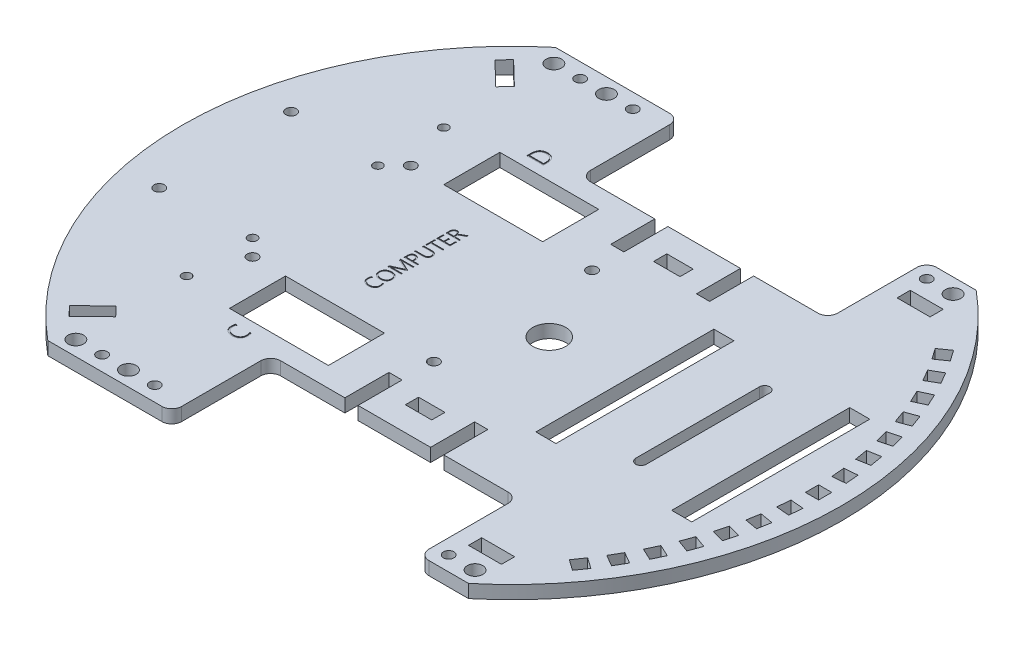
SolidWorks part; units mm, degrees
material "Oak"
ref_plane "Front Plane" through (0, 0, 0) normal (0, 0, 1) x (1, 0, 0)
ref_plane "Top Plane" through (0, 0, 0) normal (0, 1, 0) x (1, 0, 0)
ref_plane "Right Plane" through (0, 0, 0) normal (1, 0, 0) x (0, 0, -1)
sketch "Sketch1" plane through (0, 0, 0) normal (0, 1, 0) x (1, 0, 0)
  line L0 (-63.8044, 77) -> (63.8044, 77)
  line L1 (-63.8044, -77) -> (63.8044, -77)
  circle A0 centre (0, 0) radius 100
  dimension "D1" = 200
  dimension "D2" = 154
extrude "Basis" add sketch "Sketch1" along normal blind 4 contours L1 A0 L0
sketch "Sketch2" plane through (0, 4, 0) normal (0, 1, 0) x (1, 0, 0)
  line L0 (90.817, -6.1912) -> (94.8018, -6.5398)
  line L1 (91, -2) -> (95, -2)
  line L2 (91, -2) -> (91, 2)
  line L3 (91, 2) -> (95, 2)
  line L4 (95, -2) -> (95, 2)
  line L5 (90.4684, -10.176) -> (90.817, -6.1912)
  line L6 (90.4684, -10.176) -> (94.4532, -10.5246)
  line L7 (94.4532, -10.5246) -> (94.8018, -6.5398)
  line L8 (89.9208, -14.3352) -> (93.86, -15.0298)
  line L9 (89.2262, -18.2745) -> (89.9208, -14.3352)
  line L10 (89.2262, -18.2745) -> (93.1654, -18.9691)
  line L11 (93.1654, -18.9691) -> (93.86, -15.0298)
  line L12 (88.3182, -22.3702) -> (92.1819, -23.4055)
  line L13 (87.2829, -26.2339) -> (88.3182, -22.3702)
  line L14 (87.2829, -26.2339) -> (91.1466, -27.2692)
  line L15 (91.1466, -27.2692) -> (92.1819, -23.4055)
  line L16 (86.0214, -30.2349) -> (89.7802, -31.603)
  line L17 (84.6533, -33.9937) -> (86.0214, -30.2349)
  line L18 (84.6533, -33.9937) -> (88.4121, -35.3618)
  line L19 (88.4121, -35.3618) -> (89.7802, -31.603)
  line L20 (83.0479, -37.8695) -> (86.6731, -39.56)
  line L21 (81.3574, -41.4948) -> (83.0479, -37.8695)
  line L22 (81.3574, -41.4948) -> (84.9827, -43.1852)
  line L23 (84.9827, -43.1852) -> (86.6731, -39.56)
  line L24 (79.4203, -45.2159) -> (82.8844, -47.2159)
  line L25 (77.4203, -48.68) -> (79.4203, -45.2159)
  line L26 (77.4203, -48.68) -> (80.8844, -50.68)
  line L27 (80.8844, -50.68) -> (82.8844, -47.2159)
  line L28 (75.1663, -52.2182) -> (78.4429, -54.5125)
  line L29 (72.872, -55.4948) -> (75.1663, -52.2182)
  line L30 (72.872, -55.4948) -> (76.1486, -57.7891)
  line L31 (76.1486, -57.7891) -> (78.4429, -54.5125)
  line L32 (-2.896, 0) -> (91, -2) construction
  line L33 (-2.896, 0) -> (90.4684, -10.176) construction
  line L34 (90.4684, 10.176) -> (94.4532, 10.5246)
  line L35 (90.817, 6.1912) -> (90.4684, 10.176)
  line L36 (90.817, 6.1912) -> (94.8018, 6.5398)
  line L37 (94.8018, 6.5398) -> (94.4532, 10.5246)
  line L38 (89.2262, 18.2745) -> (93.1654, 18.9691)
  line L39 (89.9208, 14.3352) -> (89.2262, 18.2745)
  line L40 (89.9208, 14.3352) -> (93.86, 15.0298)
  line L41 (93.86, 15.0298) -> (93.1654, 18.9691)
  line L42 (87.2829, 26.2339) -> (91.1466, 27.2692)
  line L43 (88.3182, 22.3702) -> (87.2829, 26.2339)
  line L44 (88.3182, 22.3702) -> (92.1819, 23.4055)
  line L45 (92.1819, 23.4055) -> (91.1466, 27.2692)
  line L46 (84.6533, 33.9937) -> (88.4121, 35.3618)
  line L47 (86.0214, 30.2349) -> (84.6533, 33.9937)
  line L48 (86.0214, 30.2349) -> (89.7802, 31.603)
  line L49 (89.7802, 31.603) -> (88.4121, 35.3618)
  line L50 (81.3574, 41.4948) -> (84.9827, 43.1852)
  line L51 (83.0479, 37.8695) -> (81.3574, 41.4948)
  line L52 (83.0479, 37.8695) -> (86.6731, 39.56)
  line L53 (86.6731, 39.56) -> (84.9827, 43.1852)
  line L54 (77.4203, 48.68) -> (80.8844, 50.68)
  line L55 (79.4203, 45.2159) -> (77.4203, 48.68)
  line L56 (79.4203, 45.2159) -> (82.8844, 47.2159)
  line L57 (82.8844, 47.2159) -> (80.8844, 50.68)
  line L58 (72.872, 55.4948) -> (76.1486, 57.7891)
  line L59 (75.1663, 52.2182) -> (72.872, 55.4948)
  line L60 (75.1663, 52.2182) -> (78.4429, 54.5125)
  line L61 (78.4429, 54.5125) -> (76.1486, 57.7891)
  line L62 (-2.896, 0) -> (91, -2) construction
  line L63 (-2.896, 0) -> (90.817, 6.1912) construction
  line L64 (-2.896, 0) -> (-129.2077, 0) construction
  arc A2 (60.6142, -73.15) -> (60.6142, 73.15) centre (0, 0) ccw
  arc A3 (60.6142, -73.15) -> (60.6142, 73.15) centre (0, 0) ccw construction
  point P4 (95, 0)
  point P5 (95, 0)
  dimension "D4" = 5
  dimension "D6" = 5
  dimension "D2" = 4
  dimension "D1" = 5
  dimension "D3" = 8
  dimension "D5" = 8
extrude "Modu bracket " cut sketch "Sketch2" against normal up to surface (4 mm away) up to face at (0, 0, 0)
sketch "Sketch3" plane through (0, 4, 0) normal (0, 1, 0) x (1, 0, 0)
  line L0 (-63.8044, -77) -> (63.8044, -77) construction
  line L1 (-26.1956, -77) -> (48.8044, -77)
  line L2 (-26.1956, -77) -> (-26.1956, -47)
  line L3 (-26.1956, -47) -> (48.8044, -47)
  line L4 (48.8044, -77) -> (48.8044, -47)
  line L5 (-63.8044, 77) -> (63.8044, 77) construction
  line L6 (-26.1956, 77) -> (48.8044, 77)
  line L7 (-26.1956, 77) -> (-26.1956, 47)
  line L8 (-26.1956, 47) -> (48.8044, 47)
  line L9 (48.8044, 77) -> (48.8044, 47)
  line L10 (11.3044, -47) -> (11.3044, 47) construction
  line L11 (27.8397, 0) -> (-25.9783, 0) construction
  line L12 (7.8044, -28.15) -> (14.8044, -28.15) construction
  line L13 (7.8044, -28.15) -> (7.8044, -12.65) construction
  line L14 (7.8044, -12.65) -> (14.8044, -12.65) construction
  line L15 (14.8044, -28.15) -> (14.8044, -12.65) construction
  line L16 (7.8044, -28.15) -> (14.8044, -12.65) construction
  line L17 (7.8044, -12.65) -> (14.8044, -28.15) construction
  line L18 (0.8044, -24.15) -> (21.8044, -24.15) construction
  line L19 (0.8044, -24.15) -> (0.8044, -18.65) construction
  line L20 (0.8044, -18.65) -> (21.8044, -18.65) construction
  line L21 (21.8044, -24.15) -> (21.8044, -18.65) construction
  line L22 (0.8044, -24.15) -> (21.8044, -18.65) construction
  line L23 (0.8044, -18.65) -> (21.8044, -24.15) construction
  line L24 (0.8044, 18.65) -> (21.8044, 24.15) construction
  line L25 (0.8044, 24.15) -> (21.8044, 18.65) construction
  line L26 (7.8044, 12.65) -> (14.8044, 28.15) construction
  line L27 (7.8044, 28.15) -> (14.8044, 12.65) construction
  line L28 (21.8044, 24.15) -> (21.8044, 18.65) construction
  line L29 (0.8044, 18.65) -> (21.8044, 18.65) construction
  line L30 (0.8044, 24.15) -> (0.8044, 18.65) construction
  line L31 (0.8044, 24.15) -> (21.8044, 24.15) construction
  line L32 (14.8044, 28.15) -> (14.8044, 12.65) construction
  line L33 (7.8044, 12.65) -> (14.8044, 12.65) construction
  line L34 (7.8044, 28.15) -> (7.8044, 12.65) construction
  line L35 (7.8044, 28.15) -> (14.8044, 28.15) construction
  line L36 (7.3044, 35.65) -> (15.3044, 39.65) construction
  line L37 (7.3044, -39.65) -> (15.3044, -39.65)
  line L38 (7.3044, -39.65) -> (7.3044, -35.65)
  line L39 (7.3044, -35.65) -> (15.3044, -35.65)
  line L40 (15.3044, -39.65) -> (15.3044, -35.65)
  line L41 (7.3044, -39.65) -> (15.3044, -35.65) construction
  line L42 (7.3044, -35.65) -> (15.3044, -39.65) construction
  line L43 (7.3044, 39.65) -> (15.3044, 35.65) construction
  line L44 (15.3044, 39.65) -> (15.3044, 35.65)
  line L45 (7.3044, 35.65) -> (15.3044, 35.65)
  line L46 (7.3044, 39.65) -> (7.3044, 35.65)
  line L47 (7.3044, 39.65) -> (15.3044, 39.65)
  circle A0 centre (11.3044, 0) radius 5
  circle A1 centre (11.3044, -10.15) radius 1.6 construction
  circle A3 centre (11.3044, 10.15) radius 1.6 construction
  point P21 (11.3044, -20.4)
  point P26 (11.3044, -21.4)
  point P42 (11.3044, 21.4)
  point P43 (11.3044, 20.4)
  point P44 (11.3044, -37.65)
  point P53 (11.3044, 37.65)
  point P54 (11.3044, -28.15)
  dimension "D4" = 10
  dimension "D5" = 3.2
  dimension "D1" = 30
  dimension "D2" = 75
  dimension "D3" = 15
  dimension "D6" = 7
  dimension "D7" = 5.5
  dimension "D8" = 4
  dimension "D9" = 21
  dimension "D10" = 6
  dimension "D11" = 2.5
  dimension "D12" = 8
  dimension "D13" = 4
  dimension "D14" = 7.35
  dimension "D15" = 7.5
extrude "Cut-Extrude2" cut sketch "Sketch3" against normal through all contours L1 L4 L3 L2 | L13 L20 L15 L14 | L20 L13 L18 L15 | L20 L19 L18 L13 | L18 L13 L12 L15 | L18 L21 L20 L15 | A0 | A3 | A1 | L29 L34 L33 L32 | L31 L34 L29 L32 | L34 L31 L30 L29 | L35 L34 L31 L32 | L31 L32 L29 L28 | L47 L46 L45 L44 | L9 L6 L7 L8 | L39 L40 L37 L38
sketch "Sketch4" plane through (0, 4, 0) normal (0, 1, 0) x (1, 0, 0)
  line L0 (57.8821, -18.75) -> (57.8821, 18.75) construction
  line L1 (56.2821, -18.75) -> (56.2821, 18.75)
  line L2 (59.4821, -18.75) -> (59.4821, 18.75)
  line L4 (75.4321, -27) -> (81.5321, -27)
  line L5 (75.4321, -27) -> (75.4321, 27)
  line L6 (75.4321, 27) -> (81.5321, 27)
  line L7 (81.5321, -27) -> (81.5321, 27)
  line L8 (57.8821, -38.7193) -> (57.8821, 52.9351) construction
  line L9 (40.3321, 27) -> (34.2321, 27)
  line L10 (34.2321, -27) -> (34.2321, 27)
  line L11 (40.3321, -27) -> (34.2321, -27)
  line L12 (40.3321, -27) -> (40.3321, 27)
  arc A0 (56.2821, -18.75) -> (59.4821, -18.75) centre (57.8821, -18.75) ccw
  arc A1 (59.4821, 18.75) -> (56.2821, 18.75) centre (57.8821, 18.75) ccw
  point P2 (57.8821, 0)
  point P12 (75.4321, 0)
  dimension "D1" = 37.5
  dimension "D2" = 3.2
  dimension "D3" = 54
  dimension "D4" = 15.95
  dimension "D5" = 6.1
extrude "Cut-Extrude3" cut sketch "Sketch4" against normal up to surface (4 mm away) up to face at (11.3044, 0, 37.65)
sketch "Sketch5" plane through (0, 4, 0) normal (0, 1, 0) x (1, 0, 0)
  line L0 (11.3044, -47) -> (11.3044, 47) construction
  line L1 (-3.6956, -47.64) -> (0.3044, -47.64)
  line L2 (-3.6956, -47.64) -> (-3.6956, -33.64)
  line L3 (-3.6956, -33.64) -> (0.3044, -33.64)
  line L4 (0.3044, -47.64) -> (0.3044, -33.64)
  line L5 (-3.6956, 33.64) -> (0.3044, 33.64)
  line L6 (-3.6956, 33.64) -> (-3.6956, 47.64)
  line L7 (-3.6956, 47.64) -> (0.3044, 47.64)
  line L8 (0.3044, 33.64) -> (0.3044, 47.64)
  line L9 (-26.1956, -47) -> (48.8044, -47) construction
  line L10 (-26.1956, 47) -> (48.8044, 47) construction
  line L11 (26.3044, 47.64) -> (22.3044, 47.64)
  line L12 (22.3044, 33.64) -> (22.3044, 47.64)
  line L13 (26.3044, 33.64) -> (22.3044, 33.64)
  line L14 (26.3044, 33.64) -> (26.3044, 47.64)
  line L15 (26.3044, -33.64) -> (22.3044, -33.64)
  line L16 (22.3044, -47.64) -> (22.3044, -33.64)
  line L17 (26.3044, -47.64) -> (22.3044, -47.64)
  line L18 (26.3044, -47.64) -> (26.3044, -33.64)
  dimension "D2" = 14
  dimension "D1" = 4
  dimension "D4" = 22
  dimension "D3" = 13.36
  dimension "D5" = 67.28
extrude "Cut-Extrude4" cut sketch "Sketch5" against normal up to surface (4 mm away) up to face at (37.2821, 0, 0)
sketch "Sketch6" plane through (0, 4, 0) normal (0, 1, 0) x (1, 0, 0)
  line L0 (-95, 0) -> (-54.152, 0) construction
  line L5 (-62.5181, 57.5927) -> (-59.7394, 60.47)
  line L6 (-69.7115, 64.5392) -> (-62.5181, 57.5927)
  line L7 (-66.9328, 67.4166) -> (-69.7115, 64.5392)
  line L8 (-59.7394, 60.47) -> (-66.9328, 67.4166)
  line L9 (-59.7394, -60.47) -> (-62.5181, -57.5927)
  line L10 (53.8044, -67) -> (63.8044, -67)
  line L11 (53.8044, -67) -> (53.8044, -63)
  line L12 (53.8044, -63) -> (63.8044, -63)
  line L13 (63.8044, -67) -> (63.8044, -63)
  line L14 (48.8044, -77) -> (48.8044, -47) construction
  line L15 (48.8044, -77) -> (63.8044, -77) construction
  line L16 (53.8044, 63) -> (63.8044, 63)
  line L17 (63.8044, 67) -> (63.8044, 63)
  line L18 (53.8044, 67) -> (63.8044, 67)
  line L19 (53.8044, 67) -> (53.8044, 63)
  line L20 (-66.9328, -67.4166) -> (-59.7394, -60.47)
  line L21 (-69.7115, -64.5392) -> (-66.9328, -67.4166)
  line L22 (-62.5181, -57.5927) -> (-69.7115, -64.5392)
  circle A0 centre (0, 0) radius 95 construction
  arc A1 (-77.7809, -54.5448) -> (-77.7809, 54.5448) centre (0, 0) cw construction
  arc A2 (-63.8044, 77) -> (-63.8044, -77) centre (0, 0) ccw construction
  dimension "D5" = 5
  dimension "D1" = 10
  dimension "D2" = 4
  dimension "D3" = 5
  dimension "D4" = 10
  dimension "D6" = 44
  dimension "D8" = 10
  dimension "D9" = 4
  dimension "D10" = 44
extrude "Cut-Extrude5" cut sketch "Sketch6" against normal up to surface (4 mm away) up to face at (9.6895, 0, 0)
sketch "Sketch9" plane through (0, 4, 0) normal (0, 1, 0) x (1, 0, 0)
  line L1 (-54.6956, -24) -> (0.3044, -24) construction
  line L2 (-54.6956, -24) -> (-54.6956, 24) construction
  line L3 (-54.6956, 24) -> (0.3044, 24) construction
  line L4 (0.3044, -24) -> (0.3044, 24) construction
  line L5 (-54.6956, -24) -> (0.3044, 24) construction
  line L6 (-54.6956, 24) -> (0.3044, -24) construction
  line L7 (-59.6956, 42.5) -> (-3.6956, 42.5) construction
  line L8 (-59.6956, 42.5) -> (-59.6956, -42.5) construction
  line L9 (-59.6956, -42.5) -> (-3.6956, -42.5) construction
  line L10 (-3.6956, 42.5) -> (-3.6956, -42.5) construction
  line L11 (-59.6956, -19) -> (-3.6956, -19) construction
  line L12 (-59.6956, -19) -> (-59.6956, 39) construction
  line L13 (-59.6956, 39) -> (-3.6956, 39) construction
  line L14 (-3.6956, -19) -> (-3.6956, 39) construction
  line L16 (-3.6956, 47) -> (-3.6956, 33.64) construction
  line L18 (-59.6956, -39) -> (-3.6956, -39) construction
  line L19 (-59.6956, -39) -> (-59.6956, 19) construction
  line L20 (-59.6956, 19) -> (-3.6956, 19) construction
  line L21 (-3.6956, -39) -> (-3.6956, 19) construction
  circle A0 centre (-54.6956, -24) radius 1.6
  circle A1 centre (-54.6956, 24) radius 1.6
  circle A2 centre (0.3044, 24) radius 1.6
  circle A3 centre (0.3044, -24) radius 1.6
  circle A4 centre (-59.6956, 39) radius 1.375
  circle A6 centre (-59.6956, -19) radius 1.375
  circle A7 centre (-59.6956, 19) radius 1.375
  circle A8 centre (-59.6956, -39) radius 1.375
  point P0 (-27.1956, 0)
  point P23 (-3.6956, 0)
  dimension "D1" = 3.2
  dimension "D9" = 2.75
  dimension "D2" = 48
  dimension "D3" = 55
  dimension "D4" = 11
  dimension "D5" = 85
  dimension "D6" = 56
  dimension "D7" = 58
  dimension "D8" = 3.5
  dimension "D10" = 3.5
  dimension "D11" = 58
extrude "Cut-Extrude7" cut sketch "Sketch9" against normal up to surface (4 mm away) up to face at (-64.7254, 0, -62.5046)
sketch "Sketch10" plane through (0, 4, 0) normal (0, 1, 0) x (1, 0, 0)
  line L0 (-100, 0) -> (100, 0) construction
  line L15 (-44.6956, 41) -> (-14.6956, 41)
  line L16 (-44.6956, -24) -> (-14.6956, -24)
  line L17 (-44.6956, -24) -> (-44.6956, -41)
  line L18 (-44.6956, -41) -> (-14.6956, -41)
  line L19 (-14.6956, -24) -> (-14.6956, -41)
  line L20 (-14.6956, 24) -> (-14.6956, 41)
  line L21 (-44.6956, 24) -> (-14.6956, 24)
  line L22 (-44.6956, 24) -> (-44.6956, 41)
  arc A8 (-63.8044, 77) -> (-63.8044, -77) centre (0, 0) ccw construction
  arc A9 (63.8044, -77) -> (63.8044, 77) centre (0, 0) ccw construction
  dimension "D1" = 17
  dimension "D2" = 30
  dimension "D3" = 10
extrude "Cut-Extrude8" cut sketch "Sketch10" against normal up to surface (4 mm away) up to face at (-59.6956, 0, -37.625)
sketch "Sketch11" plane through (0, 4, 0) normal (0, 1, 0) x (1, 0, 0)
  line L0 (-87, -20) -> (-87, 20) construction
  arc A0 (-63.8044, 77) -> (-63.8044, -77) centre (0, 0) ccw construction
  circle A1 centre (-87, -20) radius 1.6
  circle A2 centre (-87, 20) radius 1.6
  point P6 (-87, 0)
  dimension "D2" = 3.2
  dimension "D1" = 40
  dimension "D3" = 87
extrude "Cut-Extrude9" cut sketch "Sketch11" against normal up to surface (4 mm away) up to face at (-29.6956, 0, 32.5)
sketch "Sketch19" plane through (0, 4, 0) normal (0, 1, 0) x (1, 0, 0)
  line L1 (-44.6956, 41) -> (-44.6956, 24) construction
  line L6 (-14.6956, 41) -> (-44.6956, 41) construction
  line L8 (-44.6956, -41) -> (-14.6956, -41) construction
  line L12 (-27.6201, 20) -> (-27.6201, -20) construction
  line L13 (-34.6956, 51) -> (-34.6956, 41) construction
  line L14 (-34.6956, -41) -> (-34.6956, -51) construction
  text T0 "COMPUTER" font "Yu Gothic UI Semilight" height 4
  text T1 "D" font "Yu Gothic UI Semilight" height 5
  text T2 "C" font "Yu Gothic UI Semilight" height 5
  point P3 (-27.6201, 0)
  dimension "D1" = 40
  dimension "D2" = 10
  dimension "D3" = 10
  dimension "D4" = 10
extrude "Cut-Extrude15" cut sketch "Sketch19" against normal blind 0.2
sketch "Sketch21" plane through (0, 4, 0) normal (0, 1, 0) x (1, 0, 0)
  line L0 (-63.8044, -77) -> (-26.1956, -77) construction
  line L1 (48.8044, -77) -> (48.8044, -47) construction
  line L2 (-100, 0) -> (100, 0) construction
  circle A0 centre (-59.8044, -72.5) radius 2.35
  circle A1 centre (-51.8244, -72.5) radius 2.35 construction
  circle A2 centre (-43.8444, -72.5) radius 2.35
  circle A3 centre (-35.8644, -72.5) radius 2.35 construction
  circle A4 centre (53.3044, -72.5) radius 2.35 construction
  circle A5 centre (61.2844, -72.5) radius 2.35
  arc A7 (63.8044, -77) -> (63.8044, 77) centre (0, 0) ccw construction
  circle A8 centre (61.2844, 72.5) radius 2.35
  circle A9 centre (53.3044, 72.5) radius 2.35 construction
  circle A10 centre (-35.8644, 72.5) radius 2.35 construction
  circle A11 centre (-43.8444, 72.5) radius 2.35
  circle A12 centre (-51.8244, 72.5) radius 2.35 construction
  circle A13 centre (-59.8044, 72.5) radius 2.35
  circle A14 centre (-51.8244, -72.5) radius 1.6
  circle A15 centre (-35.8644, -72.5) radius 1.6
  circle A16 centre (53.3044, -72.5) radius 1.6
  circle A17 centre (53.3044, 72.5) radius 1.6
  circle A18 centre (-35.8644, 72.5) radius 1.6
  circle A19 centre (-51.8244, 72.5) radius 1.6
  dimension "D1" = 4.7
  dimension "D8" = 3.2
  dimension "D2" = 4.5
  dimension "D3" = 4
  dimension "D5" = 7.98
  dimension "D6" = 4.5
  dimension "D7" = 7.98
  dimension "D4" = 4
extrude "Cut-Extrude16" cut sketch "Sketch21" against normal up to surface (4 mm away) up to face at (-87, 0, 21.6)
ref_plane "Plane1" through (0, 16, 0) normal (0, 1, 0) x (1, 0, 0)
fillet "Fillet1" radius 3 8 edges at (48.8044, 2, 77) (48.8044, 2, 47) (-26.1956, 2, 77) (-26.1956, 2, 47) (48.8044, 2, -47) (48.8044, 2, -77) (-26.1956, 2, -77) (-26.1956, 2, -47)
equation "\"WT\"=4"
equation "\"M3_hole\" = 3.2"
equation "\"D5@Sketch3\"=\"M3_hole\""
equation "\"D2@Sketch4\"=\"M3_hole\""
equation "\"D1@Sketch5\"= \"WT\""
equation "\"D2@Sketch2\"=\"WT\""
equation "\"WIG_OPENING\"=10"
equation "\"D1@Sketch9\"=\"M3_hole\""
equation "\"D2@Sketch11\"=\"M3_hole\""
equation "\"D8@Sketch21\"=\"M3_hole\""
